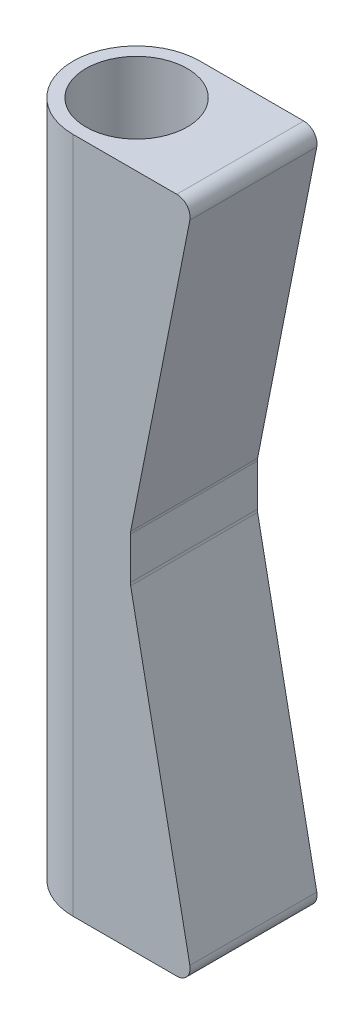
SolidWorks part; units mm, degrees
ref_plane "Front Plane" through (0, 0, 0) normal (0, 0, 1) x (1, 0, 0)
ref_plane "Top Plane" through (0, 0, 0) normal (0, 1, 0) x (1, 0, 0)
ref_plane "Right Plane" through (0, 0, 0) normal (1, 0, 0) x (0, 0, -1)
sketch "Sketch1" plane through (0, 0, 0) normal (0, 1, 0) x (1, 0, 0)
  circle A0 centre (0, 0) radius 11.4125
  circle A1 centre (0, 0) radius 14.2875
  dimension "D1" = 22.825
  dimension "D2" = 28.575
extrude "Boss-Extrude1" add sketch "Sketch1" along normal blind 152.4
ref_plane "Plane1" through (14.2875, 0, 0) normal (1, 0, 0) x (0, 0, -1)
sketch "Sketch2" plane through (14.2875, 0, 0) normal (1, 0, 0) x (0, 0, -1)
  line L1 (14.2875, 0) -> (-14.2875, 0)
  line L2 (14.2875, 0) -> (14.2875, 152.4)
  line L3 (14.2875, 152.4) -> (-14.2875, 152.4)
  line L4 (-14.2875, 0) -> (-14.2875, 152.4)
extrude "Boss-Extrude2" add sketch "Sketch2" along normal blind 12.7 separate body
sketch "Sketch3" plane through (0, 152.4, 0) normal (0, 1, 0) x (1, 0, 0)
  line L0 (14.2875, -14.2875) -> (0, -14.2875)
  line L1 (14.2875, 14.2875) -> (0, 14.2875)
  line L4 (14.2875, 14.2875) -> (14.2875, -14.2875)
  line L5 (14.2875, -14.2875) -> (26.9875, -14.2875)
  line L6 (26.9875, -14.2875) -> (26.9875, 14.2875)
  line L7 (26.9875, 14.2875) -> (14.2875, 14.2875)
  line L9 (14.2875, -14.2875) -> (26.9875, -14.2875)
  line L10 (26.9875, -14.2875) -> (26.9875, 14.2875)
  line L11 (26.9875, 14.2875) -> (14.2875, 14.2875)
  arc A0 (0, -14.2875) -> (0, 14.2875) centre (0, 0) ccw
  dimension "D1" = 0
extrude "Boss-Extrude3" add sketch "Sketch3" against normal through all
sketch "Sketch5" plane through (0, 0, 14.2875) normal (0, 0, 1) x (1, 0, 0)
  line L3 (26.9875, 0) -> (12.8972, 71.2)
  line L5 (26.9875, 0) -> (26.9875, 152.4)
  line L6 (12.8972, 71.2) -> (12.8972, 81.2)
  line L7 (12.8972, 81.2) -> (26.9875, 152.4)
  dimension "D1" = 10
  dimension "D2" = 71.2
  dimension "D3" = 71.2
extrude "Cut-Extrude1" cut sketch "Sketch5" against normal through all
fillet "Fillet1" radius 3 4 edges at (26.9875, 152.4, 0) (12.8972, 81.2, 0) (12.8972, 71.2, 0) (26.9875, 0, 0)
